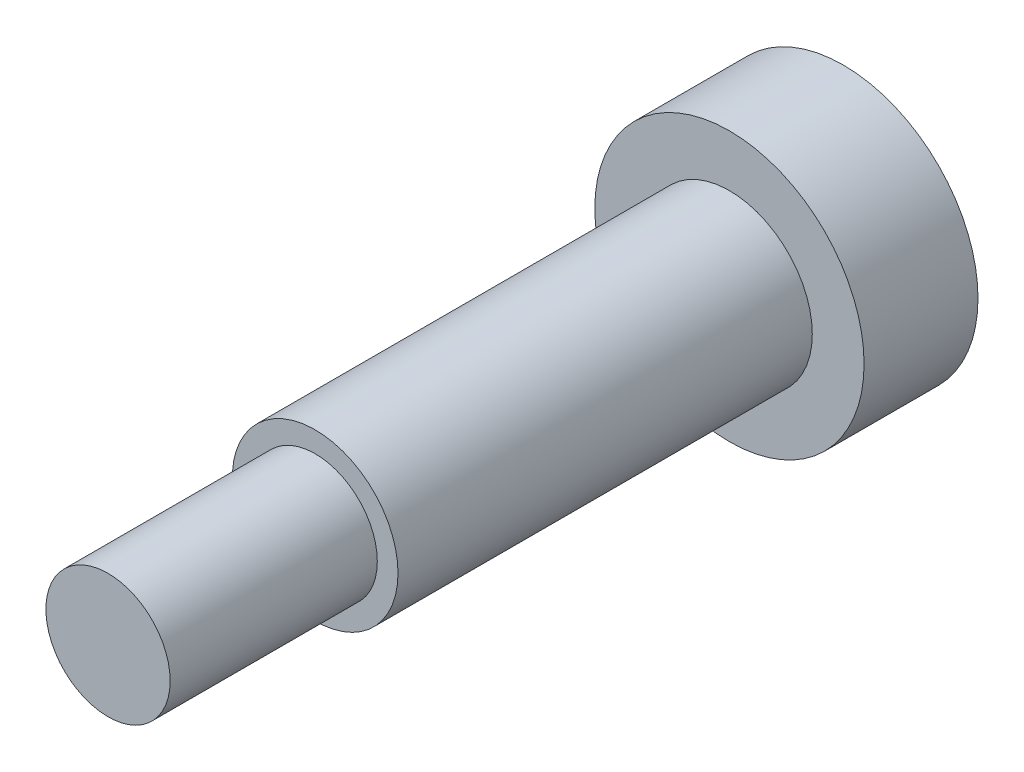
SolidWorks part; units mm, degrees
material "Stal nierdzewna (ferrytyczna)"
ref_plane "Płaszczyzna przednia" through (0, 0, 0) normal (0, 0, 1) x (1, 0, 0)
ref_plane "Płaszczyzna górna" through (0, 0, 0) normal (0, 1, 0) x (1, 0, 0)
ref_plane "Płaszczyzna prawa" through (0, 0, 0) normal (1, 0, 0) x (0, 0, -1)
sketch "Szkic1" plane through (0, 0, 0) normal (0, 0, 1) x (1, 0, 0)
  circle A0 centre (0, 0) radius 4
  dimension "D1" = 8
extrude "Dodanie-wyciągnięcie1" add sketch "Szkic1" along normal blind 20
sketch "Szkic2" plane through (0, 0, 0) normal (0, 0, -1) x (-1, 0, 0)
  circle A0 centre (0, 0) radius 6.5
  dimension "D1" = 13
extrude "Dodanie-wyciągnięcie2" add sketch "Szkic2" along normal blind 5.5 contours A0
sketch "Szkic3" plane through (0, 0, 20) normal (0, 0, 1) x (1, 0, 0)
  circle A0 centre (0, 0) radius 3
  dimension "D1" = 6
extrude "Dodanie-wyciągnięcie3" add sketch "Szkic3" along normal blind 10 contours A0
